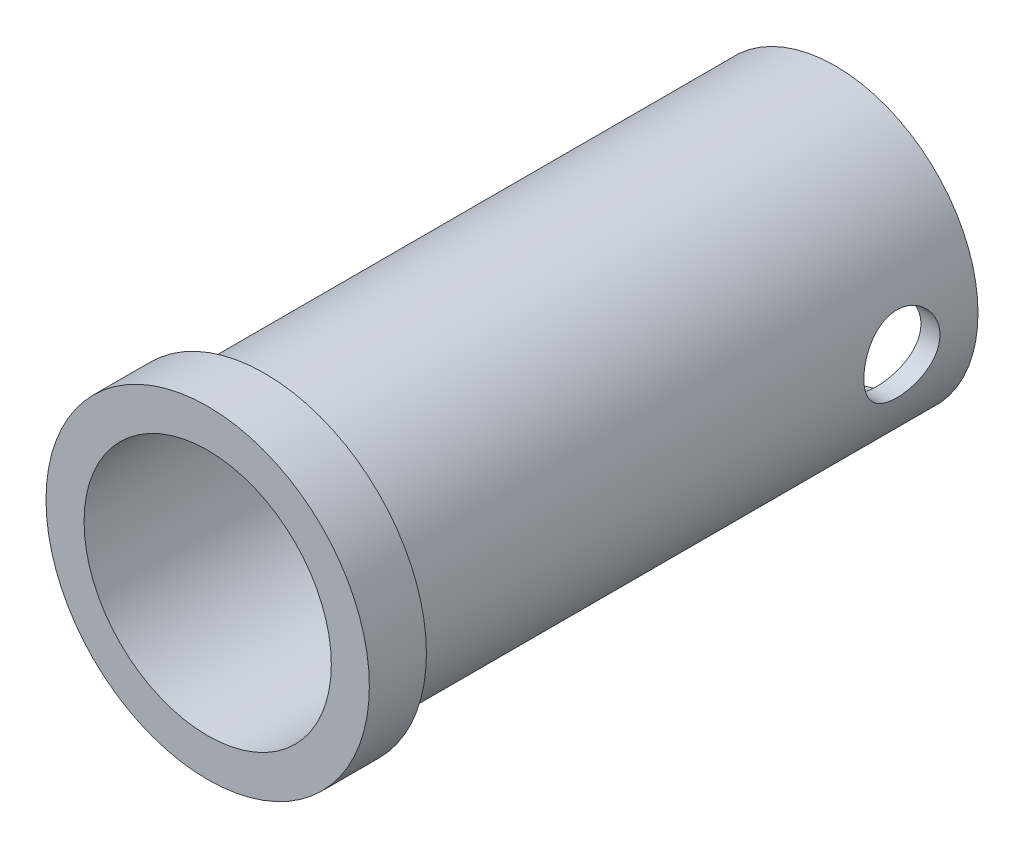
SolidWorks part; units mm, degrees
material "Gerais  - 6061-T6"
ref_plane "Plano frontal" through (0, 0, 0) normal (0, 0, 1) x (1, 0, 0)
ref_plane "Plano superior" through (0, 0, 0) normal (0, 1, 0) x (1, 0, 0)
ref_plane "Plano direito" through (0, 0, 0) normal (1, 0, 0) x (0, 0, -1)
sketch "Esboço1" plane through (0, 0, 0) normal (0, 0, 1) x (1, 0, 0)
  circle A0 centre (0, 0) radius 6.5
  circle A1 centre (0, 0) radius 8.5
  dimension "D1" = 17
  dimension "D2" = 13
extrude "Ressalto-extrusão1" add sketch "Esboço1" along normal blind 3
sketch "Esboço3" plane through (0, 0, 0) normal (0, 0, -1) x (-1, 0, 0)
  circle A0 centre (0, 0) radius 7.5
  circle A1 centre (0, 0) radius 6.5 construction
  circle A2 centre (0, 0) radius 6.5
  dimension "D1" = 15
extrude "Ressalto-extrusão3" add sketch "Esboço3" along normal blind 30
sketch "Esboço4" plane through (0, 0, 0) normal (1, 0, 0) x (0, 0, -1)
  line L0 (30, -7.5) -> (30, 7.5) construction
  circle A0 centre (26, 0) radius 2
  point P4 (30, 0)
  dimension "D2" = 4
  dimension "D1" = 4
extrude "Corte-extrusão1" cut sketch "Esboço4" against normal through all both and the other way through all
